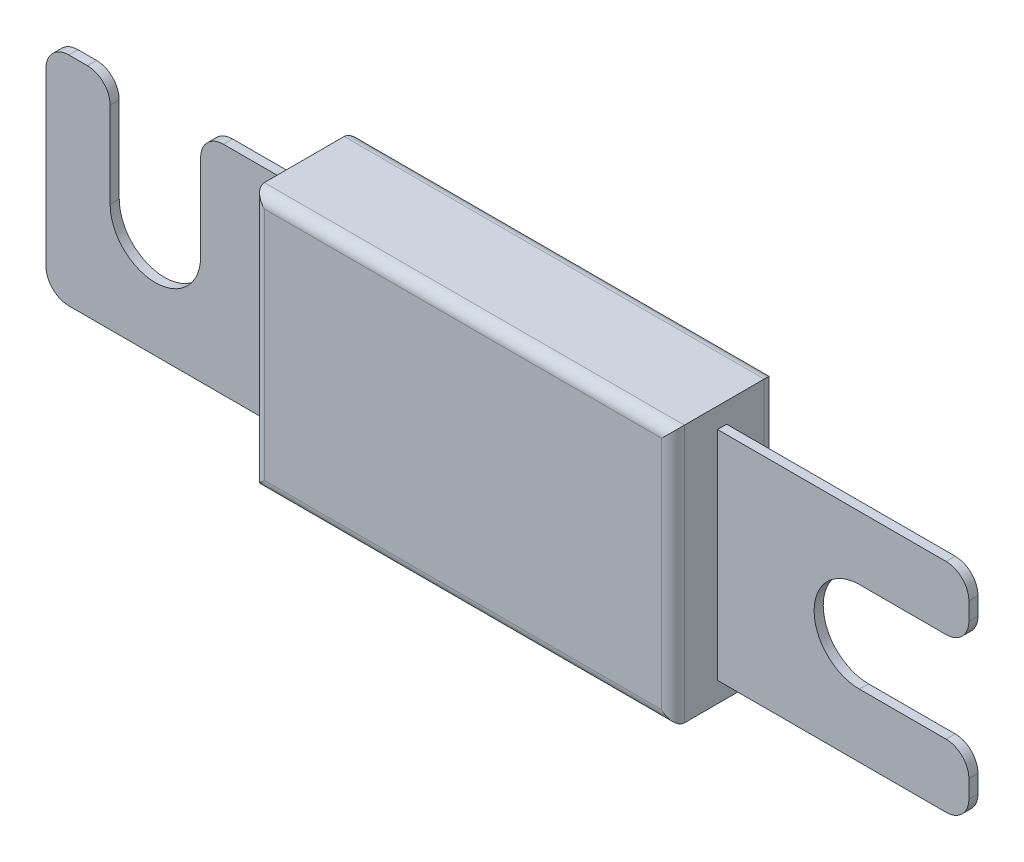
SolidWorks part; units mm, degrees
ref_plane "Alzado" through (0, 0, 0) normal (0, 0, 1) x (1, 0, 0)
ref_plane "Planta" through (0, 0, 0) normal (0, 1, 0) x (1, 0, 0)
ref_plane "Vista lateral" through (0, 0, 0) normal (1, 0, 0) x (0, 0, -1)
sketch "Croquis1" plane through (0, 0, 0) normal (0, 0, 1) x (1, 0, 0)
  line L0 (0, 2) -> (0, 17.05)
  line L1 (2, 19.05) -> (3.6212, 19.05)
  line L2 (80.91, 17.05) -> (80.91, 15.4938)
  line L3 (78.91, 0) -> (2, 0)
  line L4 (5.6212, 9.525) -> (5.6212, 17.05)
  line L5 (13.5588, 9.525) -> (13.5588, 17.05)
  line L6 (71.31, 13.4937) -> (78.91, 13.4937)
  line L7 (71.31, 5.5563) -> (78.91, 5.5563)
  line L8 (80.91, 3.5562) -> (80.91, 2)
  line L9 (15.5588, 19.05) -> (78.91, 19.05)
  arc A0 (5.6212, 9.525) -> (13.5588, 9.525) centre (9.59, 9.525) ccw
  arc A1 (71.31, 13.4937) -> (71.31, 5.5563) centre (71.31, 9.525) ccw
  arc A2 (13.5588, 17.05) -> (15.5588, 19.05) centre (15.5588, 17.05) cw
  arc A3 (0, 2) -> (2, 0) centre (2, 2) ccw
  arc A4 (80.91, 2) -> (78.91, 0) centre (78.91, 2) cw
  arc A5 (78.91, 5.5563) -> (80.91, 3.5562) centre (78.91, 3.5563) cw
  arc A6 (78.91, 13.4937) -> (80.91, 15.4938) centre (78.91, 15.4937) ccw
  arc A7 (78.91, 19.05) -> (80.91, 17.05) centre (78.91, 17.05) cw
  arc A8 (5.6212, 17.05) -> (3.6212, 19.05) centre (3.6212, 17.05) ccw
  arc A9 (0, 17.05) -> (2, 19.05) centre (2, 17.05) cw
  point P17 (13.5588, 19.05)
  point P20 (0, 0)
  point P23 (80.91, 0)
  point P26 (80.91, 5.5563)
  point P31 (80.91, 19.05)
  point P36 (0, 19.05)
  dimension "D3" = 7.9375
  dimension "D4" = 9.59
  dimension "D5" = 61.72
  dimension "D6" = 2
  dimension "D1" = 80.91
  dimension "D2" = 19.05
extrude "Saliente-Extruir1" add sketch "Croquis1" along normal blind 0.8
sketch "Croquis2" plane through (0, 0, 0.8) normal (0, 0, 1) x (1, 0, 0)
  line L0 (0, 9.525) -> (80.91, 9.525) construction
  line L1 (0, 17.05) -> (0, 2) construction
  line L2 (40.455, 9.525) -> (40.455, 19.05) construction
  line L3 (78.91, 19.05) -> (15.5588, 19.05) construction
  line L5 (58.87, 20.83) -> (22.04, 20.83)
  line L6 (58.87, 20.83) -> (58.87, -1.78)
  line L7 (58.87, -1.78) -> (22.04, -1.78)
  line L8 (22.04, 20.83) -> (22.04, -1.78)
  line L9 (58.87, 20.83) -> (22.04, -1.78) construction
  line L10 (58.87, -1.78) -> (22.04, 20.83) construction
  dimension "D1" = 36.83
  dimension "D2" = 22.61
extrude "Saliente-Extruir2" add sketch "Croquis2" along normal blind 3.9 and the other way blind 5.1
fillet "Redondeo1" radius 1 4 edges at (22.04, 9.525, -4.3) (40.455, 20.83, -4.3) (58.87, 9.525, -4.3) (40.455, -1.78, -4.3)
fillet "Redondeo2" radius 1 4 edges at (22.04, 9.525, 4.7) (40.455, 20.83, 4.7) (58.87, 9.525, 4.7) (40.455, -1.78, 4.7)
